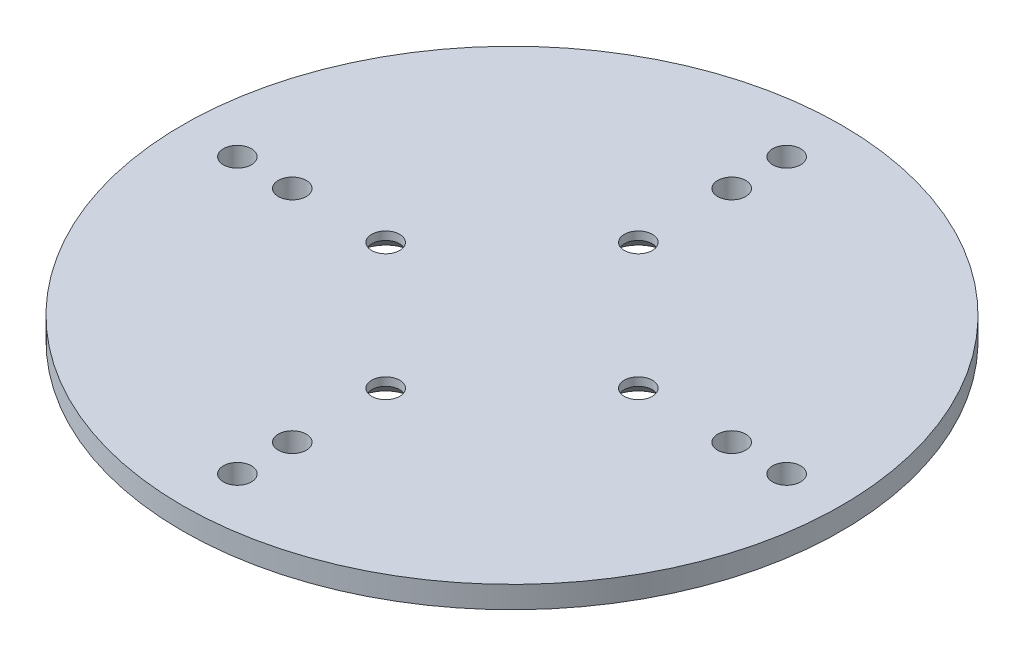
SolidWorks part; units mm, degrees
ref_plane "前视基准面" through (0, 0, 0) normal (0, 0, 1) x (1, 0, 0)
ref_plane "上视基准面" through (0, 0, 0) normal (0, 1, 0) x (1, 0, 0)
ref_plane "右视基准面" through (0, 0, 0) normal (1, 0, 0) x (0, 0, -1)
sketch "草图1" plane through (0, 0, 0) normal (0, 1, 0) x (1, 0, 0)
  circle A0 centre (0, 0) radius 60
  circle A1 centre (0, 0) radius 50 construction
  circle A2 centre (0, 50) radius 2.55
  circle A3 centre (50, 0) radius 2.55
  circle A4 centre (0, -50) radius 2.55
  circle A5 centre (-50, 0) radius 2.55
  circle A6 centre (0, 0) radius 40 construction
  circle A7 centre (0, 40) radius 2.55
  circle A8 centre (40, 0) radius 2.55
  circle A9 centre (0, -40) radius 2.55
  circle A10 centre (-40, 0) radius 2.55
  circle A11 centre (0, 0) radius 23 construction
  circle A12 centre (0, 23) radius 2.55
  circle A13 centre (23, 0) radius 2.55
  circle A14 centre (0, -23) radius 2.55
  circle A15 centre (-23, 0) radius 2.55
  point P15 (0, 0)
  point P25 (0, 0)
  point P35 (0, 0)
  dimension "D1" = 120
  dimension "D2" = 100
  dimension "D3" = 5.1
  dimension "D5" = 80
  dimension "D6" = 5.1
  dimension "D8" = 46
  dimension "D9" = 5.1
  dimension "D4" = 4
  dimension "D7" = 4
  dimension "D10" = 4
extrude "凸台-拉伸1" add sketch "草图1" along normal blind 4
chamfer "倒角1" distance 2.5 angle 45 4 edges at (0, 0, -20.45) (23, 0, 2.55) (0, 0, 25.55) (-23, 0, 2.55)
